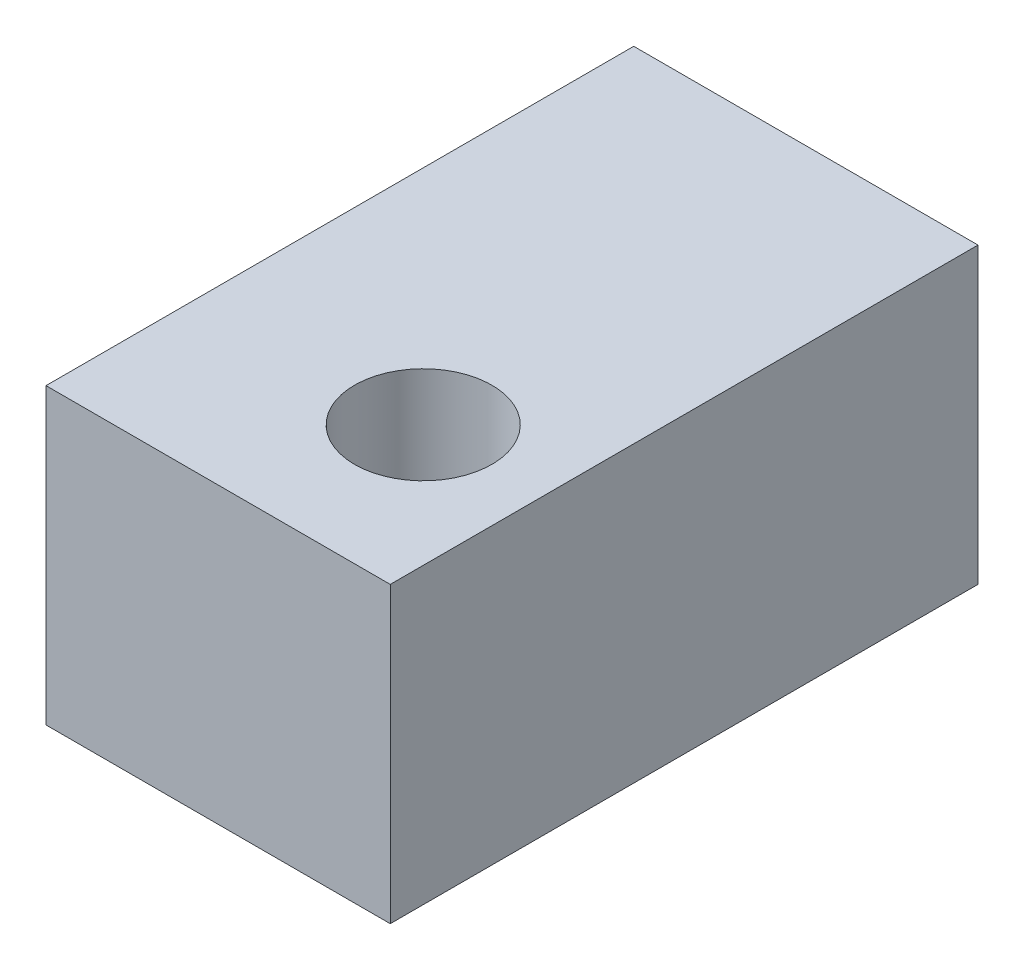
SolidWorks part; units mm, degrees
ref_plane "Plan de face" through (0, 0, 0) normal (0, 0, 1) x (1, 0, 0)
ref_plane "Plan de dessus" through (0, 0, 0) normal (0, 1, 0) x (1, 0, 0)
ref_plane "Plan de droite" through (0, 0, 0) normal (1, 0, 0) x (0, 0, -1)
sketch "Esquisse1" plane through (0, 0, 0) normal (0, 0, 1) x (1, 0, 0)
  line L1 (0, 0) -> (205, 0)
  line L2 (0, 0) -> (0, 175)
  line L3 (0, 175) -> (205, 175)
  line L4 (205, 0) -> (205, 175)
  dimension "D1" = 175
  dimension "D2" = 205
extrude "Boss.-Extru.1" add sketch "Esquisse1" along normal blind 350
sketch "Esquisse2" plane through (0, 175, 0) normal (0, 1, 0) x (1, 0, 0)
  circle A0 centre (132.503, -257.885) radius 40.8852
extrude "Enlèv. mat.-Extru.1" cut sketch "Esquisse2" against normal blind 100
